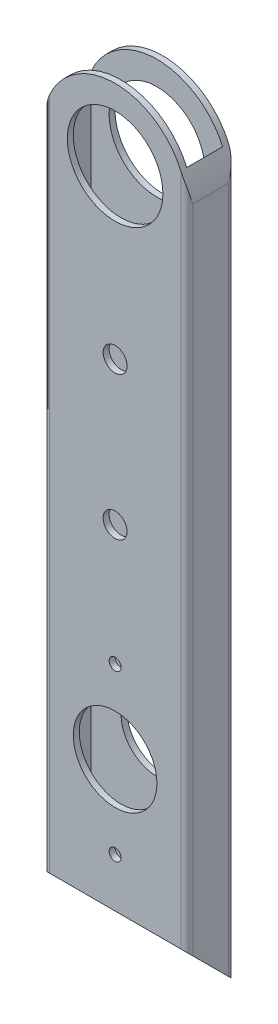
SolidWorks part; units mm, degrees
ref_plane "Front Plane" through (0, 0, 0) normal (0, 0, 1) x (1, 0, 0)
ref_plane "Top Plane" through (0, 0, 0) normal (0, 1, 0) x (1, 0, 0)
ref_plane "Right Plane" through (0, 0, 0) normal (1, 0, 0) x (0, 0, -1)
sketch "Sketch1" plane through (0, 0, 0) normal (0, 1, 0) x (1, 0, 0)
  line L0 (1.5875, 1.5875) -> (0, 1.5875) construction
  line L1 (1.5875, 0) -> (36.5125, 0)
  line L2 (0, 1.5875) -> (0, 11.1125)
  line L3 (1.5875, 12.7) -> (36.5125, 12.7)
  line L4 (38.1, 1.5875) -> (38.1, 11.1125)
  line L5 (1.5875, 1.5875) -> (36.5125, 1.5875)
  line L6 (1.5875, 1.5875) -> (1.5875, 11.1125)
  line L7 (1.5875, 11.1125) -> (36.5125, 11.1125)
  line L8 (36.5125, 1.5875) -> (36.5125, 11.1125)
  line L9 (1.5875, 1.5875) -> (1.5875, 0) construction
  line L10 (36.5125, 11.1125) -> (36.5125, 12.7) construction
  line L11 (36.5125, 11.1125) -> (38.1, 11.1125) construction
  arc A0 (1.5875, 0) -> (0, 1.5875) centre (1.5875, 1.5875) cw
  arc A1 (36.5125, 0) -> (38.1, 1.5875) centre (36.5125, 1.5875) ccw
  arc A2 (36.5125, 12.7) -> (38.1, 11.1125) centre (36.5125, 11.1125) cw
  arc A3 (0, 11.1125) -> (1.5875, 12.7) centre (1.5875, 11.1125) cw
  point P16 (0, 0)
  point P19 (38.1, 0)
  point P22 (38.1, 12.7)
  point P25 (0, 12.7)
  dimension "D4" = 1.5875
  dimension "D1" = 38.1
  dimension "D2" = 12.7
  dimension "D3" = 1.5875
extrude "Boss-Extrude1" add sketch "Sketch1" along normal blind 203.2
sketch "Sketch2" plane through (0, 0, 0) normal (0, 0, 1) x (1, 0, 0)
  line L0 (19.05, 0) -> (19.05, 203.2) construction
  line L1 (1.5875, 0) -> (36.5125, 0) construction
  line L2 (1.5875, 203.2) -> (36.5125, 203.2) construction
  line L3 (38.1, 203.2) -> (38.1, 0) construction
  line L4 (0, 184.15) -> (0, 209.55)
  line L6 (38.1, 209.55) -> (38.1, 184.15)
  line L7 (0, 209.55) -> (38.1, 209.55)
  line L8 (19.05, 69.5453) -> (40.9703, 47.625) construction
  line L9 (40.9703, 47.625) -> (19.05, 25.7047) construction
  line L10 (19.05, 47.625) -> (40.9703, 47.625) construction
  circle A0 centre (19.05, 101.6) radius 3.175
  circle A1 centre (19.05, 139.7) radius 3.175
  circle A2 centre (19.05, 184.15) radius 12.7
  arc A3 (0, 184.15) -> (38.1, 184.15) centre (19.05, 184.15) cw
  circle A4 centre (19.05, 25.7047) radius 1.5875
  circle A5 centre (19.05, 47.625) radius 9.525
  circle A6 centre (19.05, 69.5453) radius 1.5875
  dimension "D1" = 6.35
  dimension "D2" = 25.4
  dimension "D3" = 6.35
  dimension "D8" = 6.35
  dimension "D10" = 19.05
  dimension "D11" = 3.175
  dimension "D12" = 3.175
  dimension "D4" = 19.05
  dimension "D5" = 19.05
  dimension "D6" = 38.1
  dimension "D7" = 44.45
  dimension "D9" = 31
  dimension "D13" = 47.625
extrude "Cut-Extrude1" cut sketch "Sketch2" against normal through all
sketch "Sketch3" plane through (38.1, 0, 0) normal (1, 0, 0) x (0, 0, -1)
  line L0 (0, 0) -> (12.7, 0)
  line L1 (12.7, 0) -> (0, 12.7)
  line L2 (0, 191.7634) -> (0, 0) construction
  line L3 (0, 12.7) -> (0, 0)
extrude "Cut-Extrude2" cut sketch "Sketch3" against normal through all
sketch "Sketch4" plane through (0, 0, 0) normal (0, 0, 1) x (1, 0, 0)
  circle A0 centre (19.05, 47.625) radius 11.1125
  dimension "D1" = 22.225
extrude "Cut-Extrude3" cut sketch "Sketch4" against normal up to surface (1.5875 mm away) up to face at (19.05, 104.2971, -1.5875)
